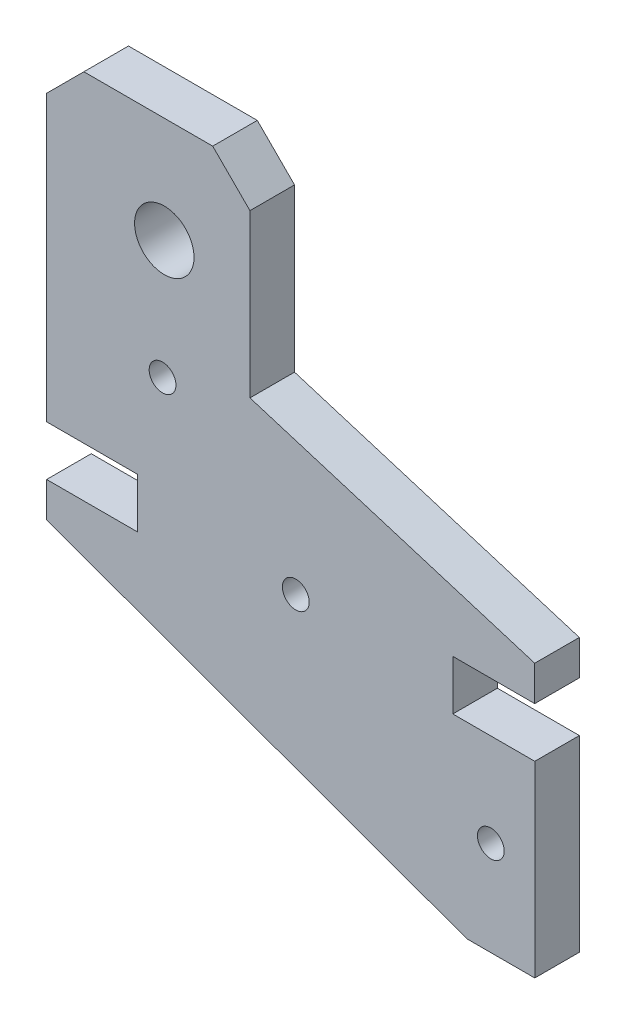
SolidWorks part; units mm, degrees
ref_plane "Plano frontal" through (0, 0, 0) normal (0, 0, 1) x (1, 0, 0)
ref_plane "Plano superior" through (0, 0, 0) normal (0, 1, 0) x (1, 0, 0)
ref_plane "Plano direito" through (0, 0, 0) normal (1, 0, 0) x (0, 0, -1)
sketch "Model" plane through (0, 0, 0) normal (0, 0, 1) x (1, 0, 0)
  line L0 (39.3386, 33.8944) -> (39.3386, 40.609)
  line L1 (39.3386, 40.609) -> (27.1157, 40.609)
  line L2 (27.1157, 29.1837) -> (27.1157, 33.8944)
  line L3 (27.1157, 33.8944) -> (39.3386, 33.8944)
  line L4 (27.1157, 40.609) -> (27.1157, 78.895)
  line L5 (27.1157, 78.895) -> (32.1269, 83.9063)
  line L6 (49.4613, 83.9063) -> (32.1269, 83.9063)
  line L7 (49.4613, 83.9063) -> (54.4725, 78.895)
  line L8 (54.4725, 57.0768) -> (54.4725, 78.895)
  line L9 (54.4725, 57.0768) -> (92.7873, 45.3198)
  line L10 (92.7873, 45.3198) -> (92.7873, 40.609)
  line L11 (92.7873, 40.609) -> (81.7648, 40.609)
  line L12 (81.7648, 40.609) -> (81.7648, 33.8944)
  line L13 (81.7648, 33.8944) -> (92.794, 33.8944)
  line L14 (92.794, 33.8944) -> (92.794, 8.6433)
  line L15 (92.794, 8.6433) -> (83.6736, 8.6433)
  line L16 (83.6736, 8.6433) -> (27.1157, 29.1837)
  circle A0 centre (86.8808, 21.3718) radius 1.8
  circle A1 centre (60.6386, 37.2517) radius 1.8
  circle A2 centre (42.7122, 53.5764) radius 1.8
  circle A3 centre (42.9467, 69.6744) radius 4
extrude "Ressalto-extrusão1" add sketch "Model" along normal blind 6
